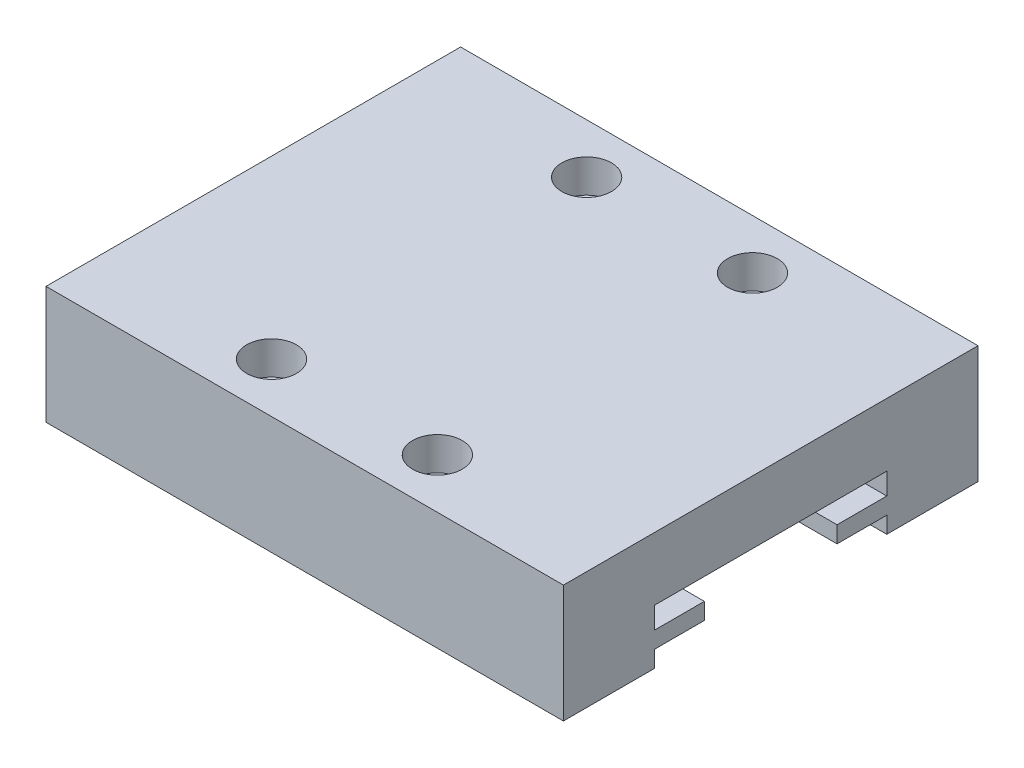
SolidWorks part; units mm, degrees
ref_plane "前视基准面" through (0, 0, 0) normal (0, 0, 1) x (1, 0, 0)
ref_plane "上视基准面" through (0, 0, 0) normal (0, 1, 0) x (1, 0, 0)
ref_plane "右视基准面" through (0, 0, 0) normal (1, 0, 0) x (0, 0, -1)
sketch "草图1" plane through (0, 0, 0) normal (0, 1, 0) x (1, 0, 0)
  line L1 (0, 0) -> (31.2, 0)
  line L2 (0, 0) -> (0, 25)
  line L3 (0, 25) -> (31.2, 25)
  line L4 (31.2, 0) -> (31.2, 25)
  dimension "D1" = 31.2
  dimension "D2" = 25
extrude "凸台-拉伸1" add sketch "草图1" along normal blind 7.1
sketch "草图2" plane through (0, 0, 0) normal (-1, 0, 0) x (0, 0, 1)
  line L0 (-12.5, 7.1) -> (-12.5, 0) construction
  line L1 (-25, 7.1) -> (0, 7.1) construction
  line L2 (-25, 0) -> (0, 0) construction
  line L3 (-19.5, 0) -> (-19.5, 1)
  line L4 (-19.5, 1) -> (-16.5, 1)
  line L5 (-16.5, 1) -> (-16.5, 2)
  line L6 (-16.5, 2) -> (-19.5, 2)
  line L7 (-19.5, 2) -> (-19.5, 3.3)
  line L8 (-19.5, 3.3) -> (-12.5, 3.3)
  line L10 (-5.5, 0) -> (-5.5, 1)
  line L11 (-5.5, 1) -> (-8.5, 1)
  line L12 (-8.5, 1) -> (-8.5, 2)
  line L13 (-8.5, 2) -> (-5.5, 2)
  line L14 (-5.5, 2) -> (-5.5, 3.3)
  line L15 (-5.5, 3.3) -> (-12.5, 3.3)
  line L16 (-19.5, 0) -> (-5.5, 0)
  dimension "D1" = 1
  dimension "D2" = 1
  dimension "D3" = 1.3
  dimension "D4" = 7
  dimension "D5" = 3
  dimension "D6" = 3
extrude "切除-拉伸1" cut sketch "草图2" against normal blind 50.9
sketch "草图3" plane through (0, 7.1, 0) normal (0, 1, 0) x (1, 0, 0)
  line L0 (15.6, 25) -> (15.6, 0) construction
  line L1 (31.2, 25) -> (0, 25) construction
  line L2 (0, 0) -> (31.2, 0) construction
  line L3 (0, 12.5) -> (31.2, 12.5) construction
  line L4 (0, 25) -> (0, 0) construction
  line L5 (31.2, 0) -> (31.2, 25) construction
  circle A0 centre (10.6, 22) radius 1.5
  circle A5 centre (20.6, 22) radius 1.5
  circle A6 centre (20.6, 3) radius 1.5
  circle A7 centre (10.6, 3) radius 1.5
  dimension "D1" = 3
  dimension "D3" = 5
  dimension "D4" = 9.5
extrude "切除-拉伸9" cut sketch "草图3" against normal blind 2
